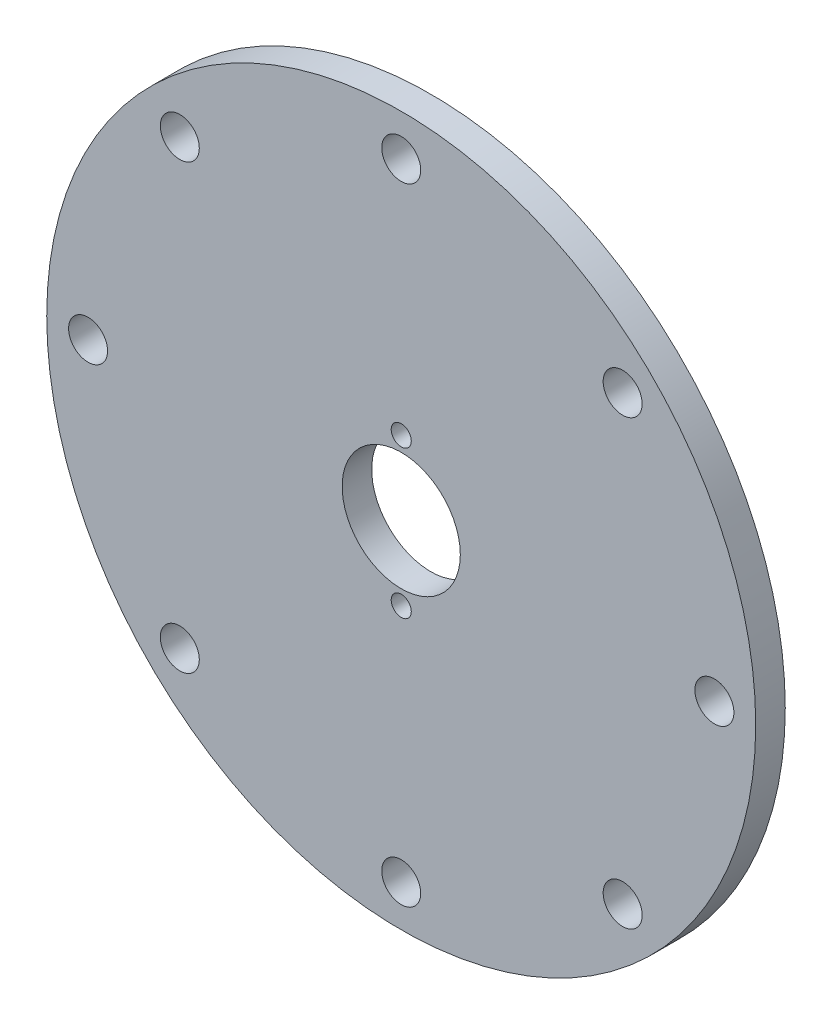
SolidWorks part; units mm, degrees
ref_plane "Front Plane" through (0, 0, 0) normal (0, 0, 1) x (1, 0, 0)
ref_plane "Top Plane" through (0, 0, 0) normal (0, 1, 0) x (1, 0, 0)
ref_plane "Right Plane" through (0, 0, 0) normal (1, 0, 0) x (0, 0, -1)
sketch "Sketch1" plane through (0, 0, 0) normal (0, 0, 1) x (1, 0, 0)
  circle A0 centre (0, 0) radius 60
  dimension "D1" = 120
extrude "Boss-Extrude1" add sketch "Sketch1" along normal blind 5
sketch "Sketch7" plane through (0, 0, 5) normal (0, 0, 1) x (1, 0, 0)
  circle A0 centre (0, 0) radius 10
  dimension "D1" = 20
extrude "Cut-Extrude1" cut sketch "Sketch7" against normal through all both and the other way through all
sketch "Sketch4" plane through (0, 0, 5) normal (0, 0, 1) x (1, 0, 0)
  point P0 (0, 12.5)
  point P2 (0, -12.5)
  dimension "D1" = 25
  dimension "D2" = 12.5
hole_wizard "M3 Clearance Hole1" positions "Sketch4" profile "Sketch3" hole size "M3" standard "ISO" end condition through all
sketch "Sketch3" plane through (0, 12.5, 5) normal (1, 0, 0) x (0, -1, 0)
  line L0 (0, 0) -> (0, 5)
  line L1 (0, 5) -> (1.7, 5)
  line L2 (1.7, 5) -> (1.7, 0)
  line L5 (1.7, 0) -> (0, 0)
  line L11 (0, -6.35) -> (0, 107.95) construction
  dimension "Thru Hole Dia." = 3.4
  dimension "Thru Hole Depth" = 5
sketch "Sketch5" plane through (0, 0, 5) normal (0, 0, 1) x (1, 0, 0)
  circle A0 centre (0, 0) radius 53 construction
  point P3 (0, 53)
  point P9 (37.4767, 37.4767)
  point P10 (53, 0)
  point P11 (37.4767, -37.4767)
  point P12 (0, -53)
  point P13 (-37.4767, -37.4767)
  point P14 (-53, 0)
  point P15 (-37.4767, 37.4767)
  dimension "D1" = 106
  dimension "D2" = 8
hole_wizard "M6 Clearance Hole1" positions "Sketch5" profile "Sketch6" hole size "M6" standard "ISO" end condition through all
sketch "Sketch6" plane through (-37.4767, 37.4767, 5) normal (1, 0, 0) x (0, -1, 0)
  line L0 (0, 0) -> (0, 5)
  line L1 (0, 5) -> (3.3, 5)
  line L2 (3.3, 5) -> (3.3, 0)
  line L5 (3.3, 0) -> (0, 0)
  line L11 (0, -6.35) -> (0, 107.95) construction
  dimension "Thru Hole Dia." = 6.6
  dimension "Thru Hole Depth" = 5
sketch "Sketch8" plane through (0, 0, 5) normal (0, 0, 1) x (1, 0, 0)
  circle A0 centre (-37.4767, 37.4767) radius 3.3 construction
  circle A1 centre (-37.4767, 37.4767) radius 3.3
